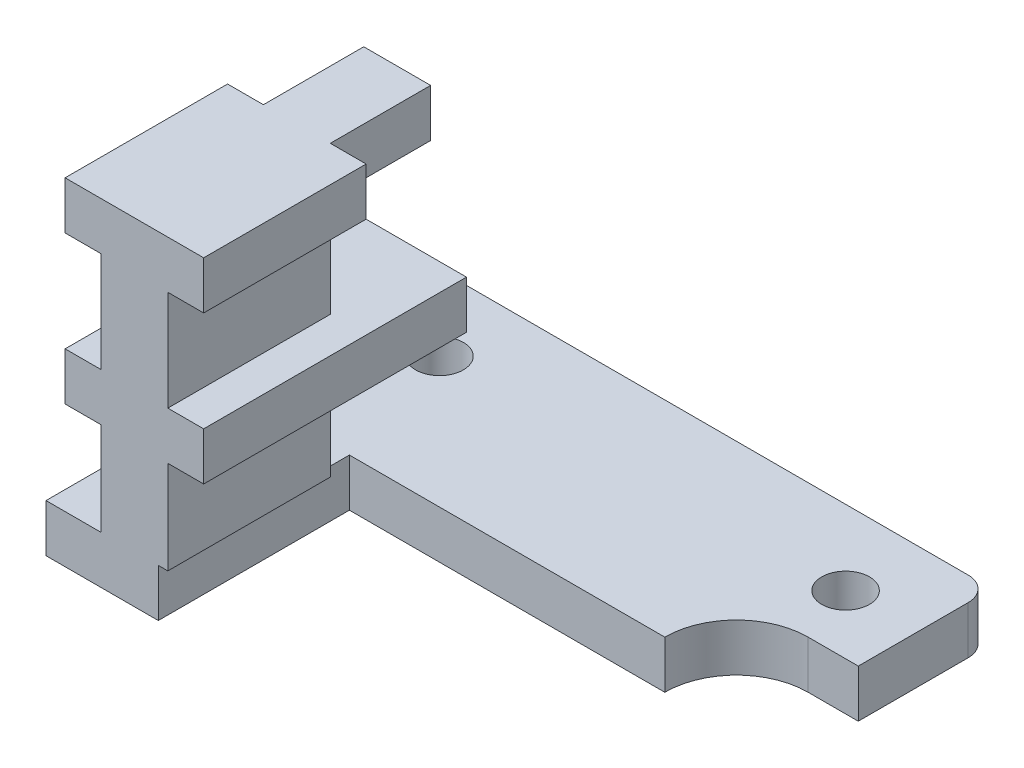
SolidWorks part; units mm, degrees
ref_plane "Front Plane" through (0, 0, 0) normal (0, 0, 1) x (1, 0, 0)
ref_plane "Top Plane" through (0, 0, 0) normal (0, 1, 0) x (1, 0, 0)
ref_plane "Right Plane" through (0, 0, 0) normal (1, 0, 0) x (0, 0, -1)
sketch "Sketch1" plane through (0, 0, 0) normal (0, 1, 0) x (1, 0, 0)
  line L0 (11.7, 3) -> (11.7, 7.6)
  line L1 (10.7, 8.6) -> (-10.3, 8.6)
  line L2 (-11.3, -8) -> (-11.3, 7.6)
  line L5 (11.7, 3) -> (9.6, 3)
  line L6 (-6.6, 0) -> (6.6, 0)
  line L7 (-6.6, 0) -> (-6.6, -8)
  line L8 (-6.6, -8) -> (-11.3, -8)
  arc A0 (9.6, 3) -> (6.6, 0) centre (9.6, 0) ccw
  circle A1 centre (8.7, 5.4696) radius 1
  circle A2 centre (-8.3, 5.4696) radius 1
  arc A3 (-10.3, 8.6) -> (-11.3, 7.6) centre (-10.3, 7.6) ccw
  arc A4 (11.7, 7.6) -> (10.7, 8.6) centre (10.7, 7.6) ccw
  point P0 (0, 0)
  point P8 (0, -3.5)
  dimension "D3" = 3
  dimension "D4" = 2
  dimension "D6" = 1
  dimension "D12" = 3.1304
  dimension "D13" = 3
  dimension "D5" = 17
  dimension "D7" = 13.2
  dimension "D8" = 16.6
  dimension "D9" = 23
  dimension "D10" = 8
  dimension "D11" = 4.7
extrude "Boss-Extrude1" add sketch "Sketch1" along normal blind 2
sketch "Sketch2" plane through (0, 0, 0) normal (0, 0, 1) x (1, 0, 0)
  line L11 (-9, 2) -> (-9, 12.1)
  line L36 (10.7, 2) -> (-10.3, 2) construction
  line L37 (-9, 12.1) -> (-10.5, 12.1)
  line L38 (-10.5, 12.1) -> (-10.5, 14.1)
  line L39 (-10.5, 14.1) -> (-4.7, 14.1)
  line L40 (-4.7, 14.1) -> (-4.7, 12.1)
  line L41 (-4.7, 12.1) -> (-6.2, 12.1)
  line L42 (-6.2, 12.1) -> (-6.2, 2)
  line L43 (-6.2, 2) -> (-9, 2)
  line L44 (-11.3, 2) -> (-11.3, 0) construction
  dimension "D1" = 10.1
  dimension "D2" = 5.8
  dimension "D3" = 2.8
  dimension "D4" = 2.3
  dimension "D5" = 2
extrude "Boss-Extrude2" add sketch "Sketch2" against normal blind 6.8 from surface at 8 starting at face at (-8.95, 1, 8)
sketch "Sketch3" plane through (0, 0, 8) normal (0, 0, 1) x (1, 0, 0)
  line L0 (-4.7, 14.1) -> (-10.5, 14.1) construction
  line L1 (-9, 12.1) -> (-6.2, 12.1)
  line L2 (-9, 12.1) -> (-9, 14.1)
  line L3 (-9, 14.1) -> (-6.2, 14.1)
  line L4 (-6.2, 12.1) -> (-6.2, 14.1)
  line L5 (-6.2, 2) -> (-6.2, 12.1) construction
  line L6 (-4.7, 12.1) -> (-4.7, 14.1) construction
  line L7 (-10.5, 5.9) -> (-4.7, 5.9)
  line L8 (-10.5, 5.9) -> (-10.5, 7.9)
  line L9 (-10.5, 7.9) -> (-4.7, 7.9)
  line L10 (-4.7, 5.9) -> (-4.7, 7.9)
  line L11 (-10.5, 14.1) -> (-10.5, 12.1) construction
  line L12 (-6.2, 12.1) -> (-4.7, 12.1) construction
  dimension "D1" = 2
  dimension "D2" = 4.2
extrude "Boss-Extrude3" add sketch "Sketch3" against normal blind 11
